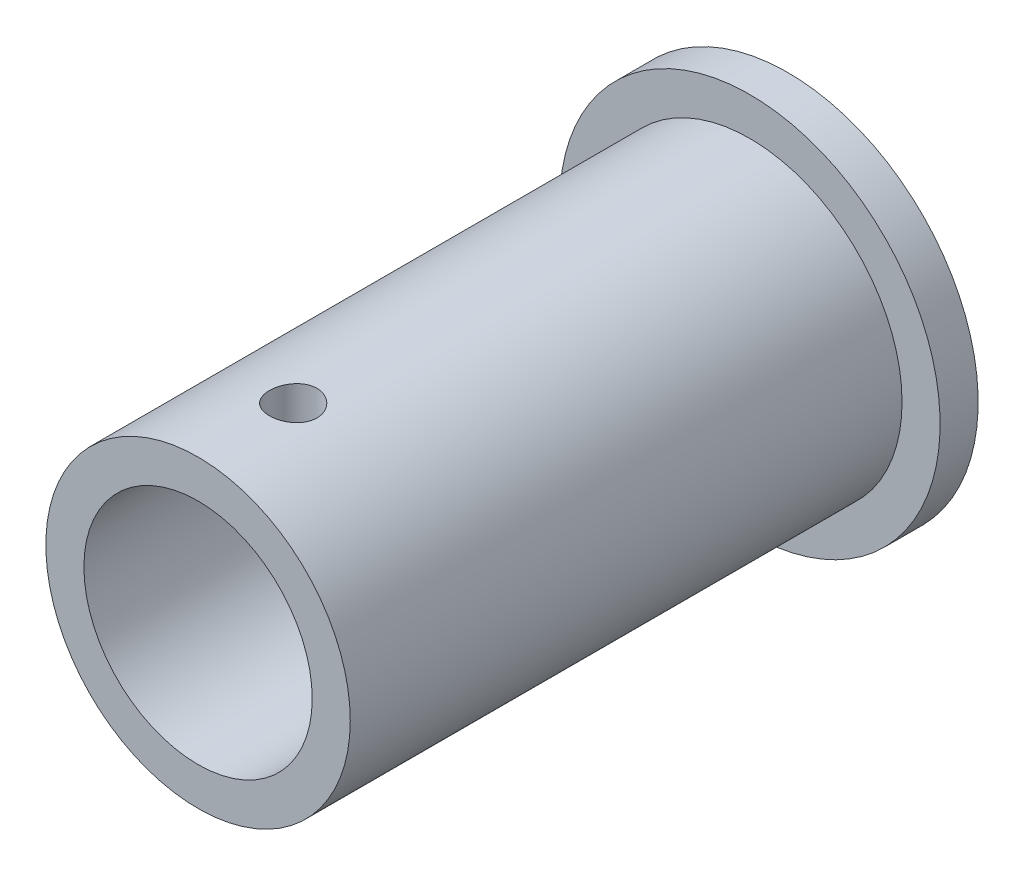
SolidWorks part; units mm, degrees
ref_plane "Front Plane" through (0, 0, 0) normal (0, 0, 1) x (1, 0, 0)
ref_plane "Top Plane" through (0, 0, 0) normal (0, 1, 0) x (1, 0, 0)
ref_plane "Right Plane" through (0, 0, 0) normal (1, 0, 0) x (0, 0, -1)
sketch "Sketch1" plane through (0, 0, 0) normal (0, 0, 1) x (1, 0, 0)
  circle A0 centre (0, 0) radius 8
  circle A1 centre (0, 0) radius 6
  dimension "D1" = 16
  dimension "D2" = 12
extrude "Boss-Extrude1" add sketch "Sketch1" along normal blind 29
sketch "Sketch2" plane through (0, 0, 0) normal (0, 0, -1) x (-1, 0, 0)
  circle A0 centre (0, 0) radius 10
  circle A3 centre (0, 0) radius 6 construction
  circle A4 centre (0, 0) radius 6
  dimension "D1" = 20
extrude "Boss-Extrude2" add sketch "Sketch2" along normal blind 2 separate body
sketch "Sketch3" plane through (0, 0, 0) normal (0, 1, 0) x (1, 0, 0)
  line L0 (-8, -29) -> (8, -29) construction
  circle A0 centre (0, -24) radius 1.25
  dimension "D1" = 2.5
  dimension "D2" = 5
extrude "Cut-Extrude1" cut sketch "Sketch3" along normal through all
